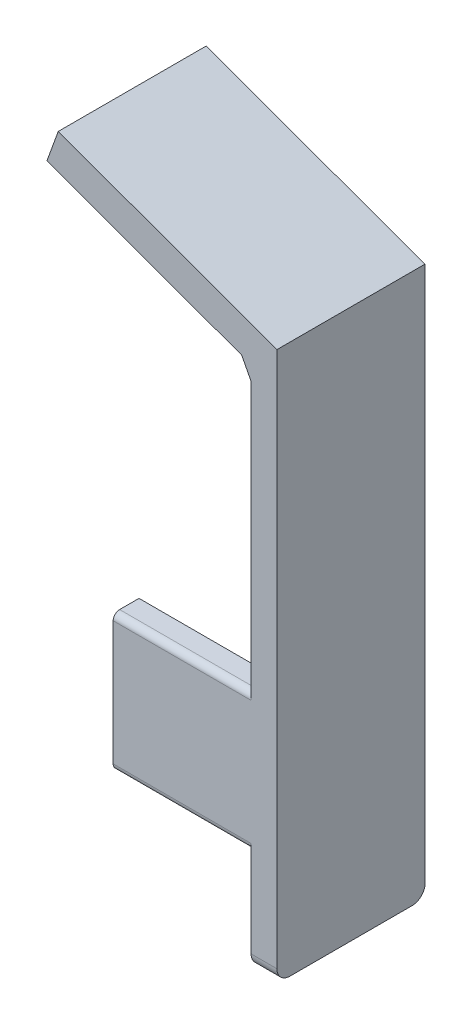
SolidWorks part; units mm, degrees
ref_plane "Plan de face" through (0, 0, 0) normal (0, 0, 1) x (1, 0, 0)
ref_plane "Plan de dessus" through (0, 0, 0) normal (0, 1, 0) x (1, 0, 0)
ref_plane "Plan de droite" through (0, 0, 0) normal (1, 0, 0) x (0, 0, -1)
sketch "Esquisse1" plane through (0, 0, 0) normal (0, 0, 1) x (1, 0, 0)
  line L0 (0, 26.549) -> (0, -58.451)
  line L1 (0, -58.451) -> (-4, -58.451)
  line L2 (-4, -58.451) -> (-4, 26.549)
  line L8 (-4, 26.549) -> (0, 26.549)
extrude "Boss.-Extru.1" add sketch "Esquisse1" along normal blind 22.93
sketch "Esquisse2" plane through (0, 0, 22.93) normal (0, 0, 1) x (1, 0, 0)
  line L4 (-33.8506, 38.8696) -> (0, 26.549)
  line L5 (0, 26.549) -> (0, 22.549)
  line L6 (0, -58.451) -> (0, 26.549) construction
  line L7 (0, 22.549) -> (-4, 22.549)
  line L8 (-4, 26.549) -> (-4, -58.451) construction
  line L9 (-4, 22.549) -> (-35.6041, 34.052)
  line L10 (-35.6041, 34.052) -> (-33.8506, 38.8696)
extrude "Boss.-Extru.5" add sketch "Esquisse2" against normal blind 22.9
sketch "Esquisse5" plane through (0, 0, 22.93) normal (0, 0, 1) x (1, 0, 0)
  line L1 (0, -58.451) -> (0, 26.549) construction
  line L2 (0, -21.471) -> (-25.35, -21.471)
  line L5 (-25.35, -21.471) -> (-25.35, -42.6526)
  line L6 (-25.35, -42.6526) -> (0, -42.6526)
  line L7 (0, -42.6526) -> (0, -21.471)
extrude "Boss.-Extru.6" add sketch "Esquisse5" against normal blind 4
sketch "Esquisse7" plane through (0, 0, 0) normal (1, 0, 0) x (0, 0, -1)
  line L0 (0, -32.571) -> (0, -21.471)
  line L1 (0, 26.549) -> (0, -58.451) construction
  line L2 (-22.93, -42.6526) -> (-22.93, -21.471) construction
  line L4 (0, -21.471) -> (0, -32.571) construction
  line L6 (0, -32.571) -> (-1.98, -32.571)
  line L7 (-1.98, -32.571) -> (-1.98, -21.471)
  line L8 (-1.98, -21.471) -> (0, -21.471)
fillet "Congé1" radius 2 2 edges at (-2, -58.451, 0) (-2, -58.451, 22.93)
fillet "Congé5" radius 1 2 edges at (-14.675, -42.6526, 22.93) (-14.675, -21.471, 22.93)
sketch "Esquisse10" plane through (-4, 0, 0) normal (-1, 0, 0) x (0, 0, 1)
  line L0 (5.5645, 13.239) -> (17.7163, 13.239) construction
  text T0 "R" font "Century Gothic" height 5
extrude "Boss.-Extru.8" add sketch "Esquisse10" along normal blind 1
sketch "Esquisse11" plane through (0, 0, 22.93) normal (0, 0, 1) x (1, 0, 0)
  line L0 (-5.4528, 23.0778) -> (-4, 20.2984)
  line L1 (-35.6041, 34.052) -> (-4, 22.549) construction
  line L2 (-4, 22.549) -> (-4, -22.471) construction
  line L3 (-4, 20.2984) -> (-0.6592, 23.0778)
  line L4 (-0.6592, 23.0778) -> (-5.4528, 23.0778)
extrude "Boss.-Extru.9" add sketch "Esquisse11" against normal blind 22.9
